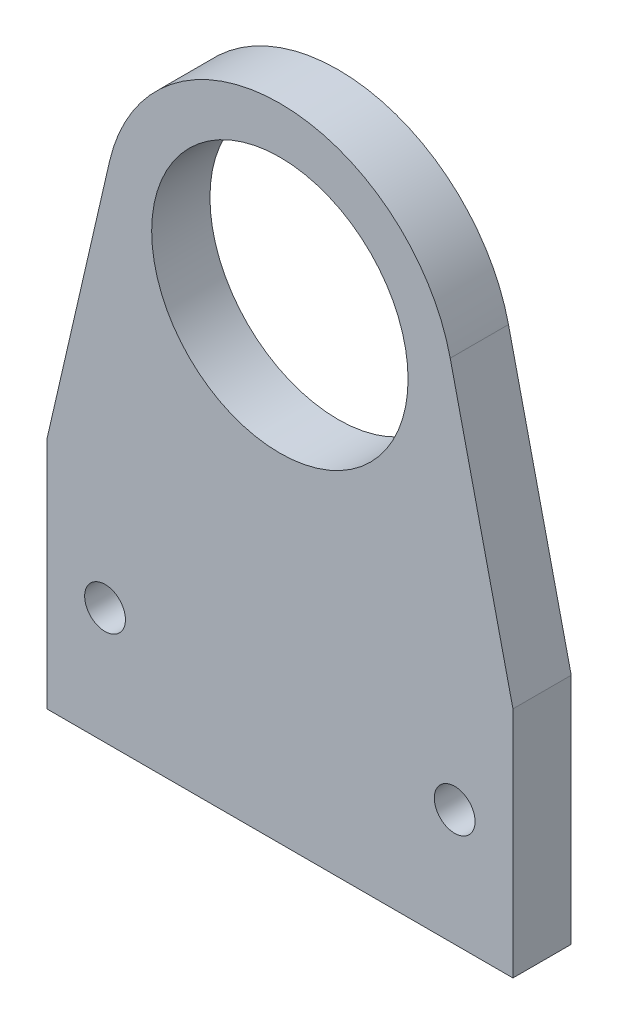
SolidWorks part; units mm, degrees
ref_plane "Front Plane" through (0, 0, 0) normal (0, 0, 1) x (1, 0, 0)
ref_plane "Top Plane" through (0, 0, 0) normal (0, 1, 0) x (1, 0, 0)
ref_plane "Right Plane" through (0, 0, 0) normal (1, 0, 0) x (0, 0, -1)
sketch "Sketch1" plane through (0, 0, 0) normal (0, 0, 1) x (1, 0, 0)
  line L0 (-14.6172, 23.3672) -> (-20, 0)
  line L1 (-20, 0) -> (20, 0) construction
  line L2 (20, 0) -> (14.6172, 23.3672)
  line L3 (0, 20) -> (0, 0) construction
  line L4 (-20, 0) -> (-20, -20)
  line L5 (-20, -20) -> (20, -20)
  line L6 (20, -20) -> (20, 0)
  line L7 (-15, -10) -> (15, -10) construction
  circle A0 centre (0, 20) radius 11
  arc A1 (14.6172, 23.3672) -> (-14.6172, 23.3672) centre (0, 20) ccw
  circle A2 centre (-15, -10) radius 1.75
  circle A3 centre (15, -10) radius 1.75
  point P14 (0, -10)
  point P15 (-20, -10)
  point P16 (0, 0)
  dimension "D1" = 22
  dimension "D2" = 4
  dimension "D3" = 3.5
  dimension "D4" = 20
  dimension "D5" = 20
  dimension "D6" = 5
  dimension "D7" = 30
extrude "Boss-Extrude1" add sketch "Sketch1" along normal blind 5
